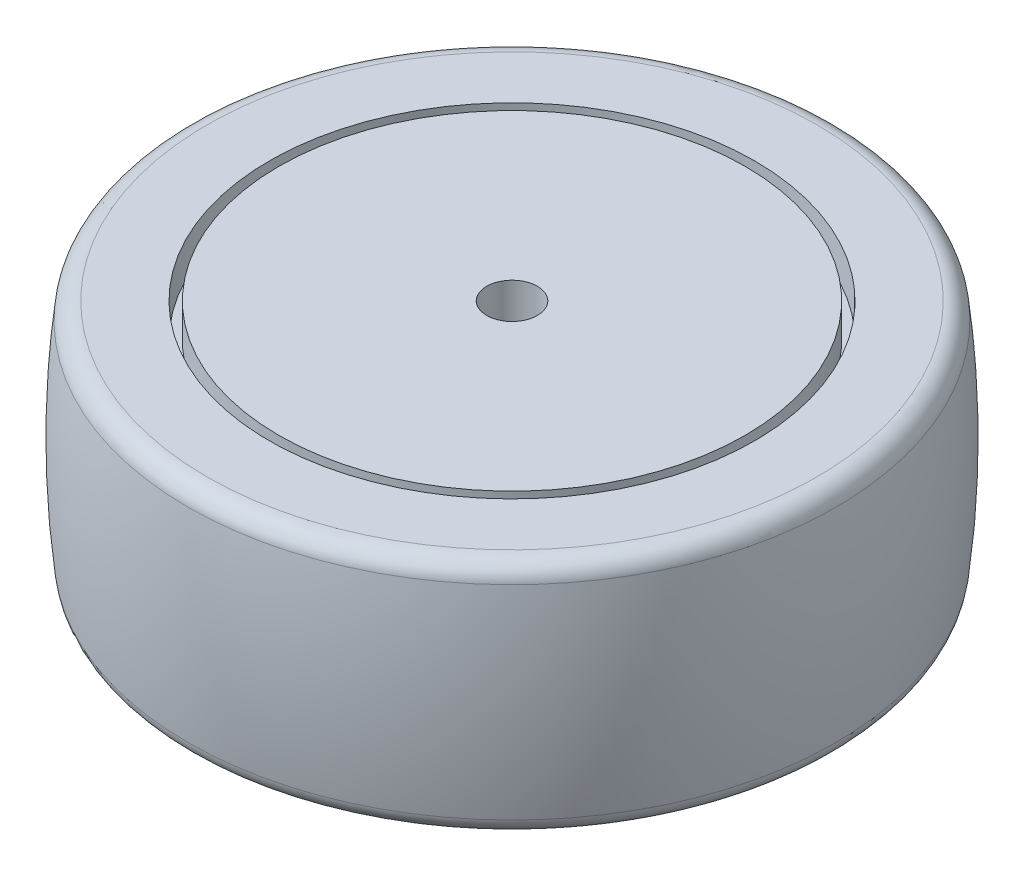
SolidWorks part; units mm, degrees
ref_plane "Front Plane" through (0, 0, 0) normal (0, 0, 1) x (1, 0, 0)
ref_plane "Top Plane" through (0, 0, 0) normal (0, 1, 0) x (1, 0, 0)
ref_plane "Right Plane" through (0, 0, 0) normal (1, 0, 0) x (0, 0, -1)
sketch "Sketch1" plane through (0, 0, 0) normal (0, 0, 1) x (1, 0, 0)
  line L0 (0, -18.75) -> (0, 18.75)
  line L1 (-50.8, 18.75) -> (-38.3, 18.75)
  line L2 (-38.3, 18.75) -> (-50.8, 18.75)
  line L3 (-38.3, 18.75) -> (-38.3, 13.2825)
  line L4 (-38.3, 13.2825) -> (-36.8, 13.2825)
  line L5 (-36.8, 13.2825) -> (-36.8, 18.75)
  line L6 (-36.8, 18.75) -> (0, 18.75)
  line L7 (0, 18.75) -> (-36.8, 18.75)
  line L8 (0, -18.75) -> (0, 120.0202) construction
  line L12 (0, 0) -> (-120.4885, 0) construction
  line L17 (0, -18.75) -> (-36.8, -18.75)
  line L18 (-36.8, -18.75) -> (0, -18.75)
  line L19 (-36.8, -13.2825) -> (-36.8, -18.75)
  line L20 (-38.3, -13.2825) -> (-36.8, -13.2825)
  line L21 (-38.3, -18.75) -> (-38.3, -13.2825)
  line L22 (-50.8, -18.75) -> (-38.3, -18.75)
  line L23 (0, -18.75) -> (-36.8, -18.75)
  line L25 (-38.3, -18.75) -> (-50.8, -18.75)
  line L26 (-38.3, -18.75) -> (-50.8, -18.75)
  arc A0 (-50.8, 18.75) -> (-50.8, -18.75) centre (90.3853, 0) ccw
  point P5 (0, 18.75)
  dimension "D1" = 37.5
  dimension "D2" = 50.8
  dimension "D3" = 12.5
  dimension "D4" = 1.5
revolve "Revolve2" add sketch "Sketch1" angle 360 about L8
fillet "Fillet1" radius 3 2 edges at (0, -18.75, -50.8) (0, 18.75, -50.8)
sketch "Sketch2" plane through (0, 18.75, 0) normal (0, 1, 0) x (1, 0, 0)
  circle A0 centre (0, 0) radius 4
  dimension "D1" = 8
extrude "Cut-Extrude1" cut sketch "Sketch2" against normal blind 137
